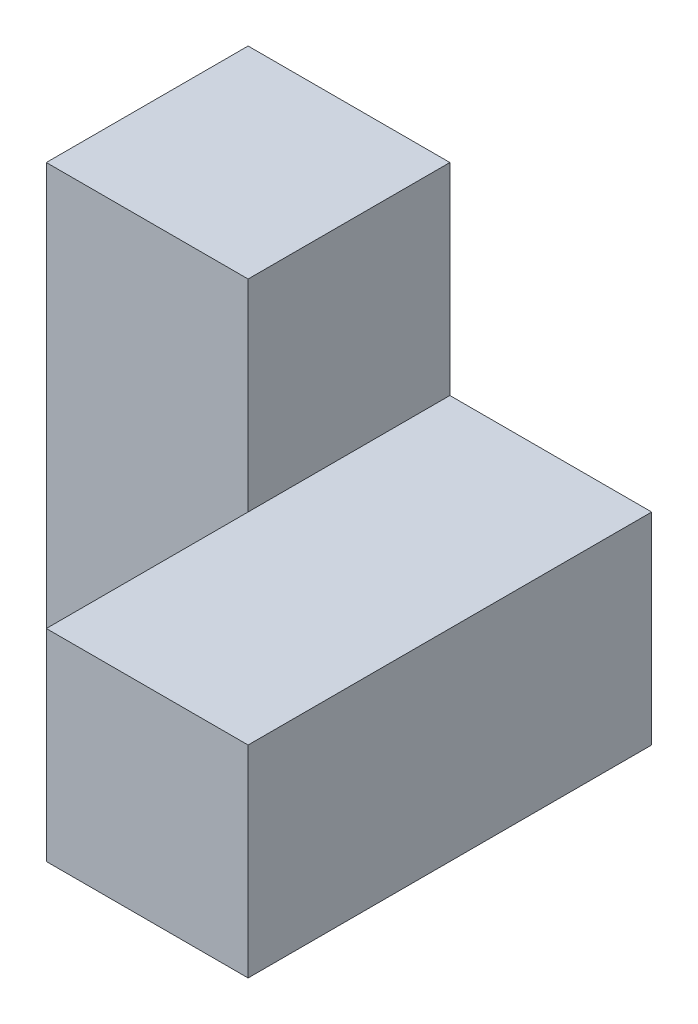
SolidWorks part; units mm, degrees
ref_plane "Front Plane" through (0, 0, 0) normal (0, 0, 1) x (1, 0, 0)
ref_plane "Top Plane" through (0, 0, 0) normal (0, 1, 0) x (1, 0, 0)
ref_plane "Right Plane" through (0, 0, 0) normal (1, 0, 0) x (0, 0, -1)
sketch "Sketch1" plane through (0, 0, 0) normal (0, 1, 0) x (1, 0, 0)
  line L1 (-25.4, -25.4) -> (25.4, -25.4)
  line L2 (-25.4, -25.4) -> (-25.4, 25.4)
  line L3 (-25.4, 25.4) -> (25.4, 25.4)
  line L4 (25.4, -25.4) -> (25.4, 25.4)
  line L5 (-25.4, -25.4) -> (25.4, 25.4) construction
  line L6 (-25.4, 25.4) -> (25.4, -25.4) construction
  point P0 (0, 0)
  dimension "D1" = 50.8
  dimension "D2" = 50.8
extrude "Boss-Extrude1" add sketch "Sketch1" along normal blind 25.4
sketch "Sketch2" plane through (0, 25.4, 0) normal (0, 1, 0) x (1, 0, 0)
  line L1 (-25.4, -25.4) -> (0, -25.4)
  line L2 (-25.4, -25.4) -> (-25.4, 0)
  line L3 (-25.4, 0) -> (0, 0)
  line L4 (0, -25.4) -> (0, 0)
extrude "Cut-Extrude1" cut sketch "Sketch2" against normal through all
sketch "Sketch3" plane through (0, 25.4, 0) normal (0, 1, 0) x (1, 0, 0)
  line L1 (-25.4, 25.4) -> (0, 25.4)
  line L2 (-25.4, 25.4) -> (-25.4, 0)
  line L3 (-25.4, 0) -> (0, 0)
  line L4 (0, 25.4) -> (0, 0)
  line L6 (-25.4, 25.4) -> (-25.4, 0)
  line L7 (-25.4, 0) -> (0, 0)
  line L8 (0, 0) -> (0, -25.4)
  line L9 (0, -25.4) -> (25.4, -25.4)
  line L10 (25.4, -25.4) -> (25.4, 25.4)
  line L11 (25.4, 25.4) -> (-25.4, 25.4)
  line L12 (-25.4, 25.4) -> (-25.4, 0)
  line L13 (-25.4, 0) -> (0, 0)
  line L14 (0, 0) -> (0, -25.4)
  line L15 (0, -25.4) -> (25.4, -25.4)
  line L16 (25.4, -25.4) -> (25.4, 25.4)
  line L17 (25.4, 25.4) -> (-25.4, 25.4)
  line M7 (-25.4, 25.4) -> (-25.4, 0)
  line M8 (-25.4, 0) -> (0, 0)
  line M12 (25.4, 25.4) -> (-25.4, 25.4)
  dimension "D1" = 0
extrude "Boss-Extrude2" add sketch "Sketch3" along normal blind 25.4 contours L4 M12 M7 M8
